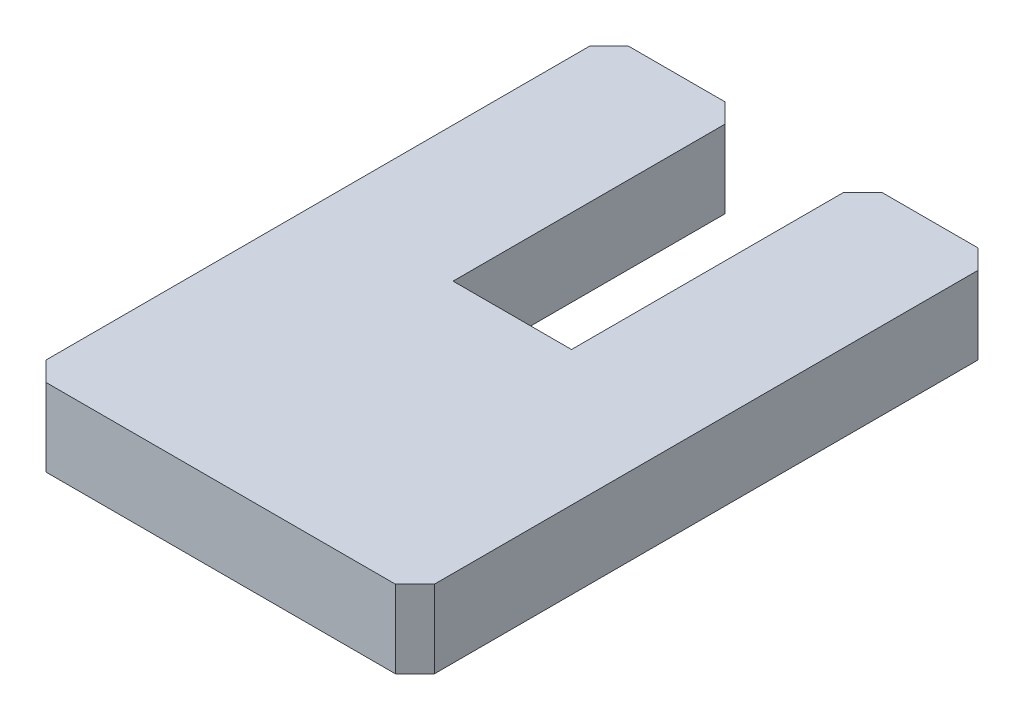
SolidWorks part; units mm, degrees
ref_plane "Vorne" through (0, 0, 0) normal (0, 0, 1) x (1, 0, 0)
ref_plane "Oben" through (0, 0, 0) normal (0, 1, 0) x (1, 0, 0)
ref_plane "Rechts" through (0, 0, 0) normal (1, 0, 0) x (0, 0, -1)
sketch "Skizze1" plane through (0, 0, 0) normal (0, 1, 0) x (1, 0, 0)
  line L1 (-10, -15) -> (10, -15)
  line L2 (-10, -15) -> (-10, 15)
  line L3 (-10, 15) -> (10, 15)
  line L4 (10, -15) -> (10, 15)
  line L5 (-10, -15) -> (10, 15) construction
  line L6 (-10, 15) -> (10, -15) construction
  point P0 (0, 0)
  dimension "D1" = 30
  dimension "D2" = 20
extrude "Aufsatz-Linear austragen1" add sketch "Skizze1" along normal blind 4
sketch "Skizze2" plane through (0, 4, 0) normal (0, 1, 0) x (1, 0, 0)
  line L0 (10, 15) -> (-10, 15) construction
  line L1 (3.0646, 0) -> (-3.0354, 0)
  line L2 (3.0646, 0) -> (3.0646, 15)
  line L3 (3.0646, 15) -> (-3.0354, 15)
  line L4 (-3.0354, 0) -> (-3.0354, 15)
  line L5 (3.0646, 0) -> (-3.0354, 15) construction
  line L6 (3.0646, 15) -> (-3.0354, 0) construction
  line L7 (0.0146, 7.5) -> (0, 0) construction
  point P0 (0.0146, 7.5)
  dimension "D1" = 6.1
  dimension "D2" = 15
extrude "Schnitt-Linear austragen1" cut sketch "Skizze2" against normal through all
chamfer "Fase1" distance 1 angle 45 6 edges at (10, 2, 15) (-10, 2, 15) (-3.0354, 2, -15) (3.0646, 2, -15) (-10, 2, -15) (10, 2, -15)
